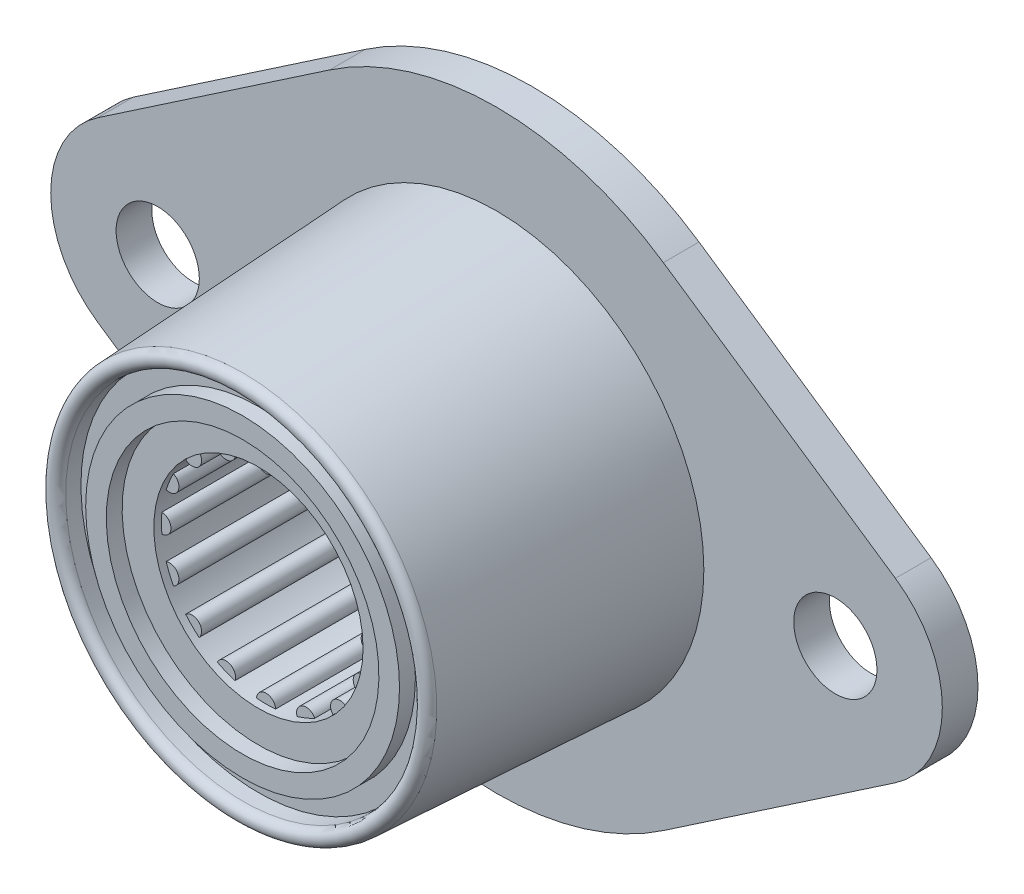
SolidWorks part; units mm, degrees
ref_plane "Front" through (0, 0, 0) normal (0, 0, 1) x (1, 0, 0)
ref_plane "Top" through (0, 0, 0) normal (0, 1, 0) x (1, 0, 0)
ref_plane "Right" through (0, 0, 0) normal (1, 0, 0) x (0, 0, -1)
sketch "Sketch1" plane through (0, 0, 0) normal (0, 0, 1) x (1, 0, 0)
  line L0 (0, 0) -> (-22.6219, 0) construction
  line L1 (0, 0) -> (22.6219, 0) construction
  line L2 (-26.6324, 5.9118) -> (-11.1404, 16.4215)
  line L3 (11.1404, 16.4215) -> (26.6324, 5.9118)
  line L4 (26.6324, -5.9118) -> (11.1404, -16.4215)
  line L5 (-11.1404, -16.4215) -> (-26.6324, -5.9118)
  line L6 (0, 19.8438) -> (0, -19.8438) construction
  arc A0 (11.1404, 16.4215) -> (-11.1404, 16.4215) centre (0, 0) ccw
  circle A1 centre (-22.6219, 0) radius 2.7781
  circle A2 centre (22.6219, 0) radius 2.7781
  arc A3 (26.6324, -5.9118) -> (26.6324, 5.9118) centre (22.6219, 0) ccw
  arc A4 (-26.6324, 5.9118) -> (-26.6324, -5.9118) centre (-22.6219, 0) ccw
  circle A5 centre (0, 0) radius 13.843
  arc A7 (-11.1404, -16.4215) -> (11.1404, -16.4215) centre (0, 0) ccw
  point P17 (0, 0)
  dimension "A" = 27.686
  dimension "Mounting Hole Dia" = 5.5562
  dimension "Overall Length" = 59.5312
  dimension "Mounting Holes" = 45.2437
  dimension "Overall Height" = 39.6875
extrude "Extrude1" add sketch "Sketch1" along normal blind 2.3813
sketch "Sketch2" plane through (0, 0, 0) normal (1, 0, 0) x (0, 0, -1)
  line L0 (0, 13.843) -> (-2.3813, 13.843)
  line L1 (-2.3813, 13.843) -> (-19.3218, 12.9552)
  line L2 (-19.2929, 11.8543) -> (-18.2769, 11.8543)
  line L3 (-18.2769, 11.8543) -> (-18.2769, 10.4783)
  line L4 (-18.2769, 6.35) -> (0, 6.35)
  line L5 (0, 6.35) -> (0, 13.843)
  line L6 (-18.2769, 10.4783) -> (-19.3357, 10.4783)
  line L7 (-19.3357, 10.4783) -> (-19.3357, 9.1022)
  line L8 (-19.3357, 9.1022) -> (-18.2769, 9.1022)
  line L9 (-18.2769, 10.4783) -> (-18.2769, 9.1022) construction
  line L10 (0, 0) -> (-18.2769, 0) construction
  line L11 (-18.2769, 0) -> (-18.2769, 6.35) construction
  line L12 (-18.2769, 7.7261) -> (-18.2769, 6.35)
  line L13 (-18.2769, 9.1022) -> (-18.2769, 7.7261)
  line L14 (0, 16.4215) -> (0, 19.8438) construction
  line L15 (0, 16.4215) -> (0, 19.8438) construction
  line L16 (-19.2929, 12.4051) -> (-19.8438, 12.4051) construction
  arc A0 (-19.3218, 12.9552) -> (-19.8438, 12.4051) centre (-19.2929, 12.4051) ccw
  arc A1 (-19.8438, 12.4051) -> (-19.2929, 11.8543) centre (-19.2929, 12.4051) ccw
  dimension "F" = 19.8438
  dimension "Shaft Dia" = 12.7
  dimension "D3" = 1.1008
  dimension "D4" = 1.016
  dimension "D5" = 3
  dimension "D2" = 0.508
  dimension "D6" = 1.3761
revolve "Revolve1" add sketch "Sketch2" angle 360 about L10
sketch "Sketch3" plane through (0, 0, 18.2769) normal (0, 0, 1) x (1, 0, 0)
  line L0 (0, 0) -> (6.985, 0) construction
  arc A0 (-3.2481, 6.1839) -> (-4.4702, 5.3673) centre (0, 0) ccw
  arc A1 (6.9561, 0.6343) -> (6.9561, -0.6343) centre (6.985, 0) ccw
  circle A2 centre (0, 0) radius 6.35 construction
  arc A3 (6.6694, -2.0759) -> (6.1839, -3.2481) centre (6.4533, -2.673) ccw
  arc A4 (5.3673, -4.4702) -> (4.4702, -5.3673) centre (4.9391, -4.9391) ccw
  arc A5 (3.2481, -6.1839) -> (2.0759, -6.6694) centre (2.673, -6.4533) ccw
  arc A6 (0.6343, -6.9561) -> (-0.6343, -6.9561) centre (0, -6.985) ccw
  arc A7 (-2.0759, -6.6694) -> (-3.2481, -6.1839) centre (-2.673, -6.4533) ccw
  arc A8 (-4.4702, -5.3673) -> (-5.3673, -4.4702) centre (-4.9391, -4.9391) ccw
  arc A9 (-6.1839, -3.2481) -> (-6.6694, -2.0759) centre (-6.4533, -2.673) ccw
  arc A10 (-6.9561, -0.6343) -> (-6.9561, 0.6343) centre (-6.985, 0) ccw
  arc A11 (-6.6694, 2.0759) -> (-6.1839, 3.2481) centre (-6.4533, 2.673) ccw
  arc A12 (-5.3673, 4.4702) -> (-4.4702, 5.3673) centre (-4.9391, 4.9391) ccw
  arc A13 (-3.2481, 6.1839) -> (-2.0759, 6.6694) centre (-2.673, 6.4533) ccw
  arc A14 (-0.6343, 6.9561) -> (0.6343, 6.9561) centre (0, 6.985) ccw
  arc A15 (2.0759, 6.6694) -> (3.2481, 6.1839) centre (2.673, 6.4533) ccw
  arc A16 (4.4702, 5.3673) -> (5.3673, 4.4702) centre (4.9391, 4.9391) ccw
  arc A17 (6.1839, 3.2481) -> (6.6694, 2.0759) centre (6.4533, 2.673) ccw
  arc A18 (-5.3673, 4.4702) -> (-6.1839, 3.2481) centre (0, 0) ccw
  arc A19 (-6.6694, 2.0759) -> (-6.9561, 0.6343) centre (0, 0) ccw
  arc A20 (-6.9561, -0.6343) -> (-6.6694, -2.0759) centre (0, 0) ccw
  arc A21 (-6.1839, -3.2481) -> (-5.3673, -4.4702) centre (0, 0) ccw
  arc A22 (-4.4702, -5.3673) -> (-3.2481, -6.1839) centre (0, 0) ccw
  arc A23 (-2.0759, -6.6694) -> (-0.6343, -6.9561) centre (0, 0) ccw
  arc A24 (0.6343, -6.9561) -> (2.0759, -6.6694) centre (0, 0) ccw
  arc A25 (3.2481, -6.1839) -> (4.4702, -5.3673) centre (0, 0) ccw
  arc A26 (5.3673, -4.4702) -> (6.1839, -3.2481) centre (0, 0) ccw
  arc A27 (6.6694, -2.0759) -> (6.9561, -0.6343) centre (0, 0) ccw
  arc A28 (6.9561, 0.6343) -> (6.6694, 2.0759) centre (0, 0) ccw
  arc A29 (6.1839, 3.2481) -> (5.3673, 4.4702) centre (0, 0) ccw
  arc A30 (4.4702, 5.3673) -> (3.2481, 6.1839) centre (0, 0) ccw
  arc A31 (2.0759, 6.6694) -> (0.6343, 6.9561) centre (0, 0) ccw
  arc A32 (-0.6343, 6.9561) -> (-2.0759, 6.6694) centre (0, 0) ccw
  dimension "D1" = 13.97
extrude "Cut-Extrude2" cut sketch "Sketch3" against normal through all
sketch "Sketch4" plane through (0, 0, 18.2769) normal (0, 0, 1) x (1, 0, 0)
  circle A0 centre (0, 0) radius 6.985
extrude "Cut-Extrude3" cut sketch "Sketch4" against normal blind 0.508
sketch "Sketch5" plane through (0, 0, 0) normal (0, 0, -1) x (-1, 0, 0)
  circle A0 centre (0, 0) radius 6.985
  arc A1 (2.0759, 6.6694) -> (0.6343, 6.9561) centre (0, 0) ccw construction
extrude "Cut-Extrude4" cut sketch "Sketch5" against normal blind 0.508
equation "\"D1@Sketch3\"=\"Shaft Dia@Sketch2\"*1.1"
equation "\"D3@Sketch2\"=\"D6@Sketch2\"/1.25"
